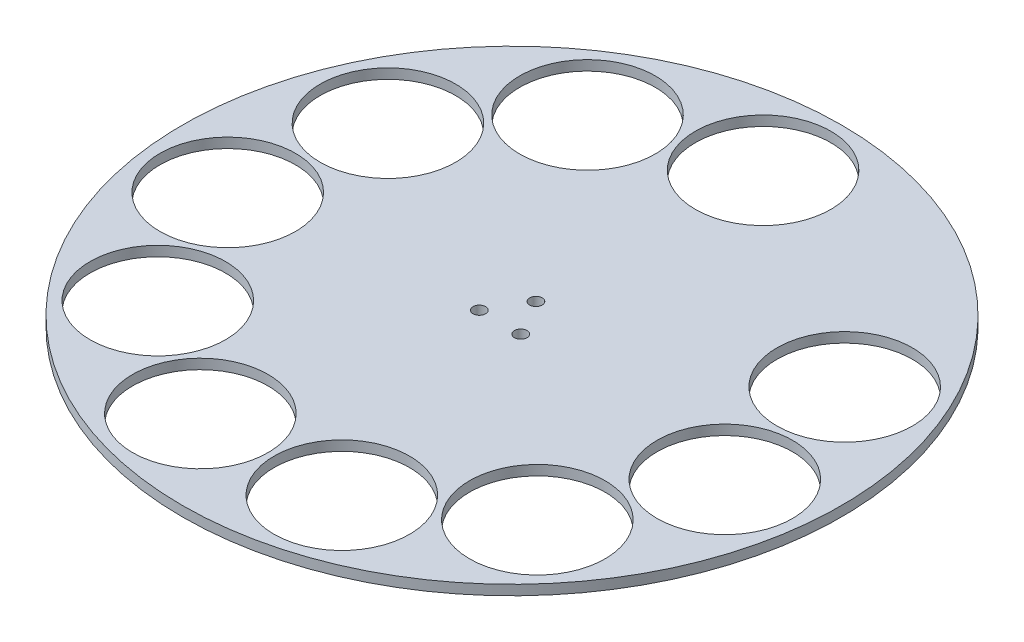
SolidWorks part; units mm, degrees
ref_plane "Front Plane" through (0, 0, 0) normal (0, 0, 1) x (1, 0, 0)
ref_plane "Top Plane" through (0, 0, 0) normal (0, 1, 0) x (1, 0, 0)
ref_plane "Right Plane" through (0, 0, 0) normal (1, 0, 0) x (0, 0, -1)
sketch "Sketch2" plane through (0, 0, 0) normal (0, 1, 0) x (1, 0, 0)
  circle A0 centre (0, 0) radius 105
  circle A1 centre (0, 80) radius 21.59
  circle A3 centre (72.7706, 33.2332) radius 21.59
  circle A4 centre (79.1857, -11.3852) radius 21.59
  circle A5 centre (60.46, -52.3889) radius 21.59
  circle A6 centre (22.5386, -76.7594) radius 21.59
  circle A7 centre (-22.5386, -76.7594) radius 21.59
  circle A8 centre (-60.46, -52.3889) radius 21.59
  circle A9 centre (-79.1857, -11.3852) radius 21.59
  circle A10 centre (-72.7706, 33.2332) radius 21.59
  circle A13 centre (-43.2513, 67.3003) radius 21.59
  circle A14 centre (43.2513, 67.3003) radius 21.59 [skipped]
  circle A15 centre (0, 7.62) radius 2
  circle A16 centre (6.5991, -3.81) radius 2
  circle A17 centre (-6.5991, -3.81) radius 2
  point P26 (0, 0)
  point P35 (0, 0)
  dimension "D1" = 210
  dimension "D2" = 43.18
  dimension "D5" = 4
  dimension "D3" = 80
  dimension "D6" = 7.62
  dimension "D4" = 11
  dimension "D7" = 3
extrude "Boss-Extrude2" add sketch "Sketch2" along normal blind 3.175
equation "\"D2@Sketch2\"=43.18"
